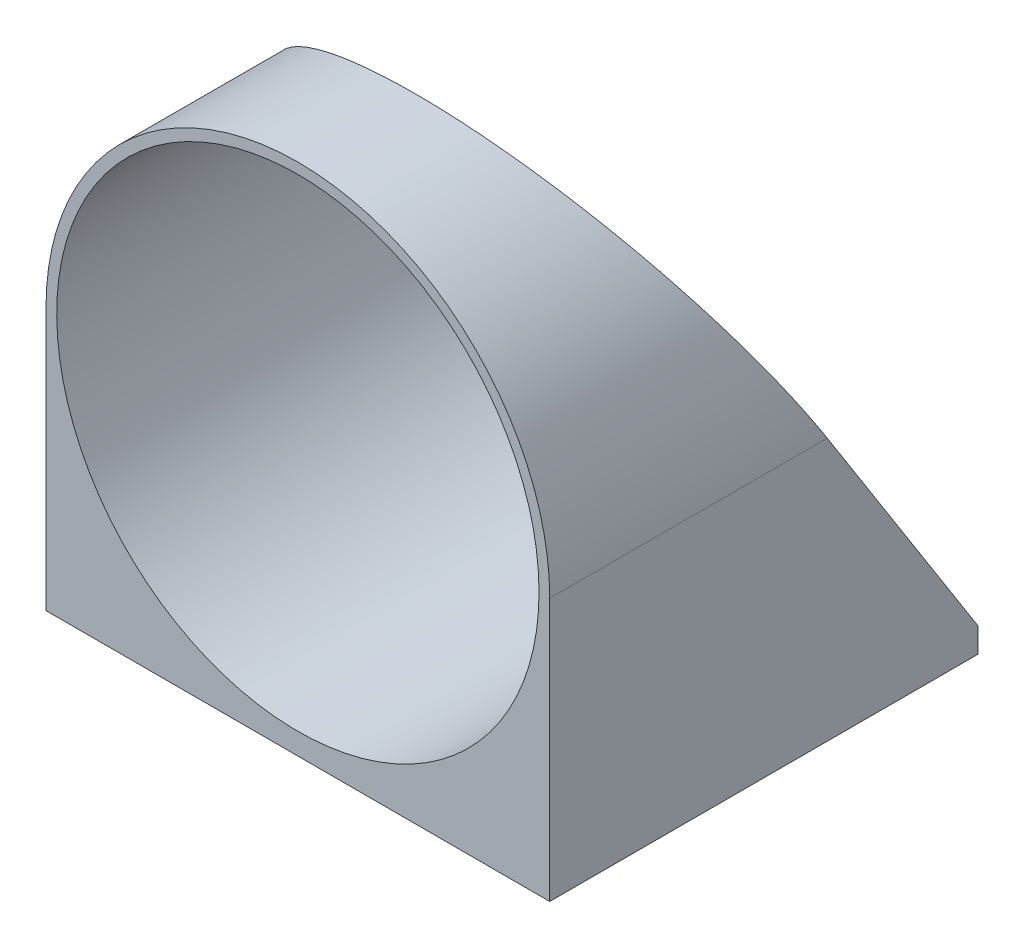
SolidWorks part; units mm, degrees
ref_plane "Front Plane" through (0, 0, 0) normal (0, 0, 1) x (1, 0, 0)
ref_plane "Top Plane" through (0, 0, 0) normal (0, 1, 0) x (1, 0, 0)
ref_plane "Right Plane" through (0, 0, 0) normal (1, 0, 0) x (0, 0, -1)
sketch "Sketch1" plane through (0, 0, 0) normal (0, 0, 1) x (1, 0, 0)
  circle A0 centre (0, 0) radius 22.225 construction
  circle A1 centre (0, 0) radius 22.225 construction
  circle A2 centre (0, 0) radius 23.525
  circle A3 centre (0, 0) radius 22.525
  dimension "D1" = 1.3
  dimension "D2" = 0.3
extrude "Boss-Extrude1" add sketch "Sketch1" along normal blind 40 from vertex
sketch "Sketch4" plane through (0, 0, -816.5402) normal (0, 0, 1) x (1, 0, 0)
  line L0 (23.525, 0) -> (23.525, -23.525)
  line L1 (23.525, -23.525) -> (0, -23.525)
  line L2 (0, -23.525) -> (-23.525, -23.525)
  line L3 (-23.525, -23.525) -> (-23.525, 0)
  line L5 (-23.525, -23.525) -> (23.525, -23.525)
  line L6 (-23.525, -23.525) -> (-23.525, -24.525)
  line L7 (-23.525, -24.525) -> (23.525, -24.525)
  line L8 (23.525, -23.525) -> (23.525, -24.525)
  circle A0 centre (0, 0) radius 23.525 construction
  circle M2 centre (0, 0) radius 23.525
  dimension "D1" = 1
extrude "Boss-Extrude2" add sketch "Sketch4" against normal blind 40 contours L8 L1 L2 L6 L7 | L1 L0 M2 | L3 L2 M2
sketch "Sketch3" plane through (0, 0, 0) normal (1, 0, 0) x (0, 0, -1)
  line L0 (828.3668, 22.225) -> (856.5402, -22.225) construction
  line L1 (827.5428, 23.525) -> (856.5402, -22.225)
  line L2 (856.5402, 23.525) -> (816.5402, 23.525) construction
  line L4 (856.5402, 0) -> (856.5402, 23.525) construction
  line L5 (856.5402, -22.225) -> (856.5402, 23.525)
  line L6 (856.5402, 23.525) -> (827.5428, 23.525)
extrude "Cut-Extrude1" cut sketch "Sketch3" against normal through all both and the other way through all
